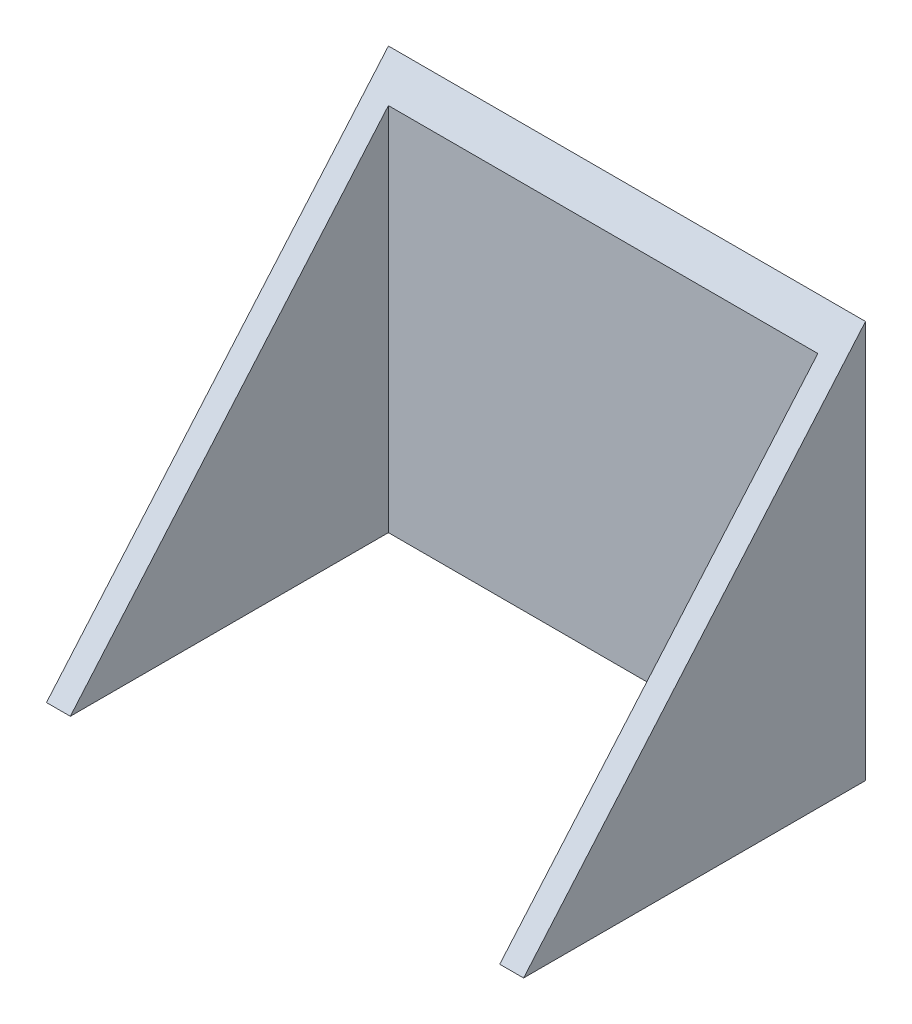
SolidWorks part; units mm, degrees
ref_plane "Front Plane" through (0, 0, 0) normal (0, 0, 1) x (1, 0, 0)
ref_plane "Top Plane" through (0, 0, 0) normal (0, 1, 0) x (1, 0, 0)
ref_plane "Right Plane" through (0, 0, 0) normal (1, 0, 0) x (0, 0, -1)
sketch "Sketch1" plane through (0, 0, 0) normal (0, 1, 0) x (1, 0, 0)
  line L1 (-60, -3) -> (60, -3)
  line L2 (-60, -3) -> (-60, 3)
  line L3 (-60, 3) -> (60, 3)
  line L4 (60, -3) -> (60, 3)
  line L5 (-60, -3) -> (60, 3) construction
  line L6 (-60, 3) -> (60, -3) construction
  line L7 (-60, -3) -> (-54, -3)
  line L8 (-60, -3) -> (-60, -83)
  line L9 (-60, -83) -> (-54, -83)
  line L10 (-54, -3) -> (-54, -83)
  line L11 (60, -3) -> (54, -3)
  line L12 (60, -3) -> (60, -83)
  line L13 (60, -83) -> (54, -83)
  line L14 (54, -3) -> (54, -83)
  point P0 (0, 0)
  dimension "D1" = 120
  dimension "D2" = 6
  dimension "D3" = 6
  dimension "D4" = 80
  dimension "D5" = 80
extrude "Boss-Extrude1" add sketch "Sketch1" along normal blind 100 contours L1 L14 L13 L12 | L1 L4 L3 L2 | L10 L1 L8 L9
sketch "Sketch2" plane through (-60, 0, 0) normal (-1, 0, 0) x (0, 0, 1)
  line L0 (83, 0) -> (-3, 100)
  line L1 (-3, 100) -> (83, 100)
  line L2 (83, 100) -> (83, 0)
extrude "Cut-Extrude1" cut sketch "Sketch2" against normal up to surface (120 mm away) up to face at (60, 50, 40)
